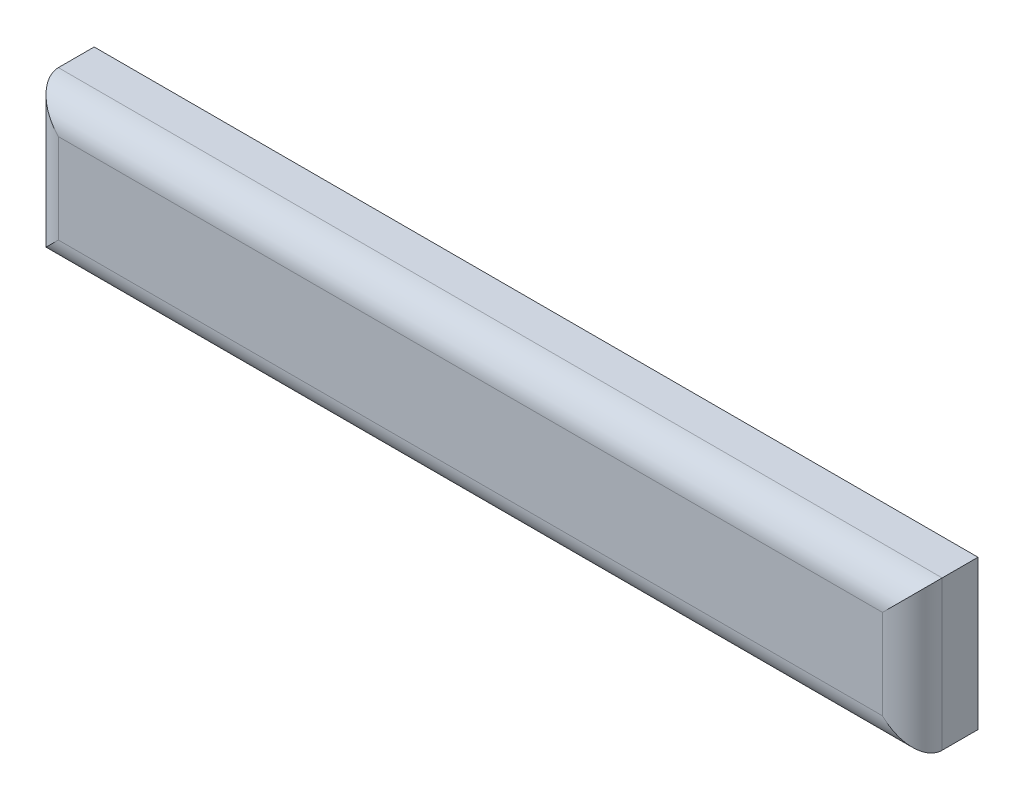
SolidWorks part; units mm, degrees
ref_plane "Alzado" through (0, 0, 0) normal (0, 0, 1) x (1, 0, 0)
ref_plane "Planta" through (0, 0, 0) normal (0, 1, 0) x (1, 0, 0)
ref_plane "Vista lateral" through (0, 0, 0) normal (1, 0, 0) x (0, 0, -1)
sketch "Croquis1" plane through (0, 0, 0) normal (0, 0, 1) x (1, 0, 0)
  line L0 (67.5, -35) -> (10, -35) construction
  line L1 (67.5, -28.75) -> (67.5, -41.25) construction
  line L2 (10, -41.25) -> (10, -28.75) construction
  line L4 (112.75, -22.5) -> (-35.25, -22.5)
  line L5 (112.75, -22.5) -> (112.75, -47.5)
  line L6 (112.75, -47.5) -> (-35.25, -47.5)
  line L7 (-35.25, -22.5) -> (-35.25, -47.5)
  line L8 (112.75, -22.5) -> (-35.25, -47.5) construction
  line L9 (112.75, -47.5) -> (-35.25, -22.5) construction
  point P6 (38.75, -35)
  dimension "D1" = 148
  dimension "D2" = 25
extrude "Saliente-Extruir1" add sketch "Croquis1" along normal blind 11
fillet "Redondeo1" radius 5 4 edges at (-35.25, -35, 11) (38.75, -22.5, 11) (112.75, -35, 11) (38.75, -47.5, 11)
sketch "Croquis2" plane through (0, 0, 0) normal (0, 0, -1) x (-1, 0, 0)
  line L0 (-38.75, -47.5) -> (-38.75, -22.5) construction
  line L1 (35.25, -47.5) -> (-112.75, -47.5) construction
  line L2 (-112.75, -22.5) -> (35.25, -22.5) construction
  line L3 (-38.75, -22.5) -> (-38.75, -35) construction
  line L4 (-38.75, -35) -> (-73.75, -35) construction
  circle A0 centre (-73.75, -35) radius 5.875
  circle A1 centre (-3.75, -35) radius 5.875
  dimension "D2" = 11.75
  dimension "D1" = 35
extrude "Cortar-Extruir1" cut sketch "Croquis2" against normal blind 9
sketch "Croquis3" plane through (0, 0, 0) normal (0, 0, -1) x (-1, 0, 0)
  line L0 (-38.75, -47.5) -> (-38.75, -22.5) construction
  line L1 (35.25, -47.5) -> (-112.75, -47.5) construction
  line L2 (-112.75, -22.5) -> (35.25, -22.5) construction
  circle A0 centre (-73.75, -35) radius 7
  circle A1 centre (-3.75, -35) radius 7
  dimension "D1" = 14
extrude "Cortar-Extruir2" cut sketch "Croquis3" against normal blind 4.5
